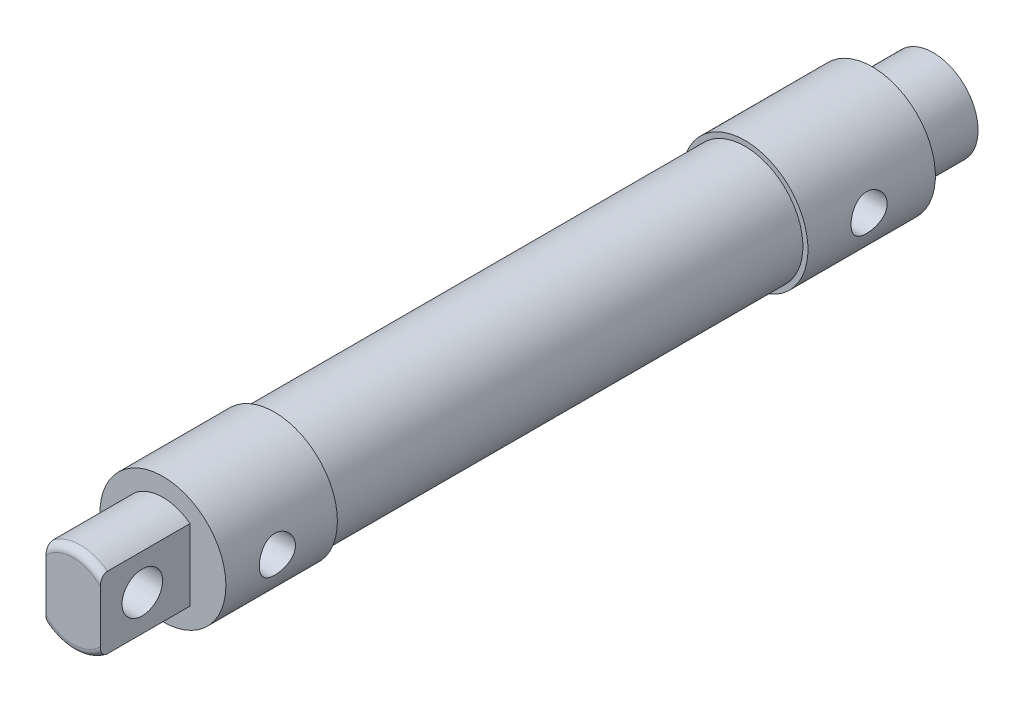
SolidWorks part; units mm, degrees
ref_plane "Front Plane" through (0, 0, 0) normal (0, 0, 1) x (1, 0, 0)
ref_plane "Top Plane" through (0, 0, 0) normal (0, 1, 0) x (1, 0, 0)
ref_plane "Right Plane" through (0, 0, 0) normal (1, 0, 0) x (0, 0, -1)
sketch "Sketch1" plane through (0, 0, 0) normal (0, 0, 1) x (1, 0, 0)
  circle A0 centre (0, 0) radius 10.16
  dimension "D1" = 20.32
extrude "Boss-Extrude1" add sketch "Sketch1" along normal blind 82.55
sketch "Sketch2" plane through (0, 0, 82.55) normal (0, 0, 1) x (1, 0, 0)
  circle A0 centre (0, 0) radius 11.049
  dimension "D1" = 22.098
extrude "Boss-Extrude2" add sketch "Sketch2" along normal blind 19.558 separate body
sketch "Sketch3" plane through (0, 0, 102.108) normal (0, 0, 1) x (1, 0, 0)
  line L0 (0, -7.874) -> (0, 7.874) construction
  line L1 (4.7625, -6.2704) -> (4.7625, 6.2704)
  line L2 (-4.7625, -6.2704) -> (-4.7625, 6.2704)
  line L3 (4.7625, -7.874) -> (4.7625, 7.874) construction
  line L4 (-4.7625, -7.874) -> (-4.7625, 7.874) construction
  arc A0 (4.7625, 6.2704) -> (-4.7625, 6.2704) centre (0, 0) ccw
  arc A1 (-4.7625, -6.2704) -> (4.7625, -6.2704) centre (0, 0) ccw
  dimension "D1" = 15.748
  dimension "D2" = 4.7625
  dimension "D3" = 4.7625
extrude "Boss-Extrude3" add sketch "Sketch3" along normal blind 15.748
sketch "Sketch4" plane through (4.7625, 0, 0) normal (1, 0, 0) x (0, 0, -1)
  line L0 (-117.856, 0) -> (-114.046, 0) construction
  line L1 (-117.856, -6.2704) -> (-117.856, 6.2704) construction
  circle A0 centre (-110.49, 0) radius 3.556
  dimension "D1" = 3.81
extrude "Cut-Extrude1" cut sketch "Sketch4" against normal up to next (9.525 mm away)
fillet "Fillet1" radius 1.27 2 edges at (0, 7.874, 117.856) (0, -7.874, 117.856)
sketch "Sketch5" plane through (0, 0, 0) normal (0, 0, -1) x (-1, 0, 0)
  circle A0 centre (0, 0) radius 11.049 construction
  circle A1 centre (0, 0) radius 11.049
extrude "Boss-Extrude4" add sketch "Sketch5" along normal blind 22.352
sketch "Sketch6" plane through (0, 0, -22.352) normal (0, 0, -1) x (-1, 0, 0)
  circle A0 centre (0, 0) radius 7.874
  dimension "D1" = 15.748
extrude "Boss-Extrude5" add sketch "Sketch6" along normal blind 10.668
sketch "Sketch7" plane through (0, 0, -33.02) normal (0, 0, -1) x (-1, 0, 0)
  circle A0 centre (0, 0) radius 3.175
  dimension "D1" = 6.35
extrude "Cut-Extrude2" cut sketch "Sketch7" against normal blind 124.968
ref_plane "Plane1" through (0, 0, 0) normal (1, 0, 0) x (0, 0, -1)
sketch "Sketch8" plane through (0, 0, 0) normal (1, 0, 0) x (0, 0, -1)
  circle A0 centre (-93.0761, 0) radius 3.175
  circle A1 centre (10.7398, 0) radius 3.175
  dimension "D1" = 6.35
  dimension "D2" = 6.35
extrude "Cut-Extrude3" cut sketch "Sketch8" along normal up to next (11.049 mm away)
